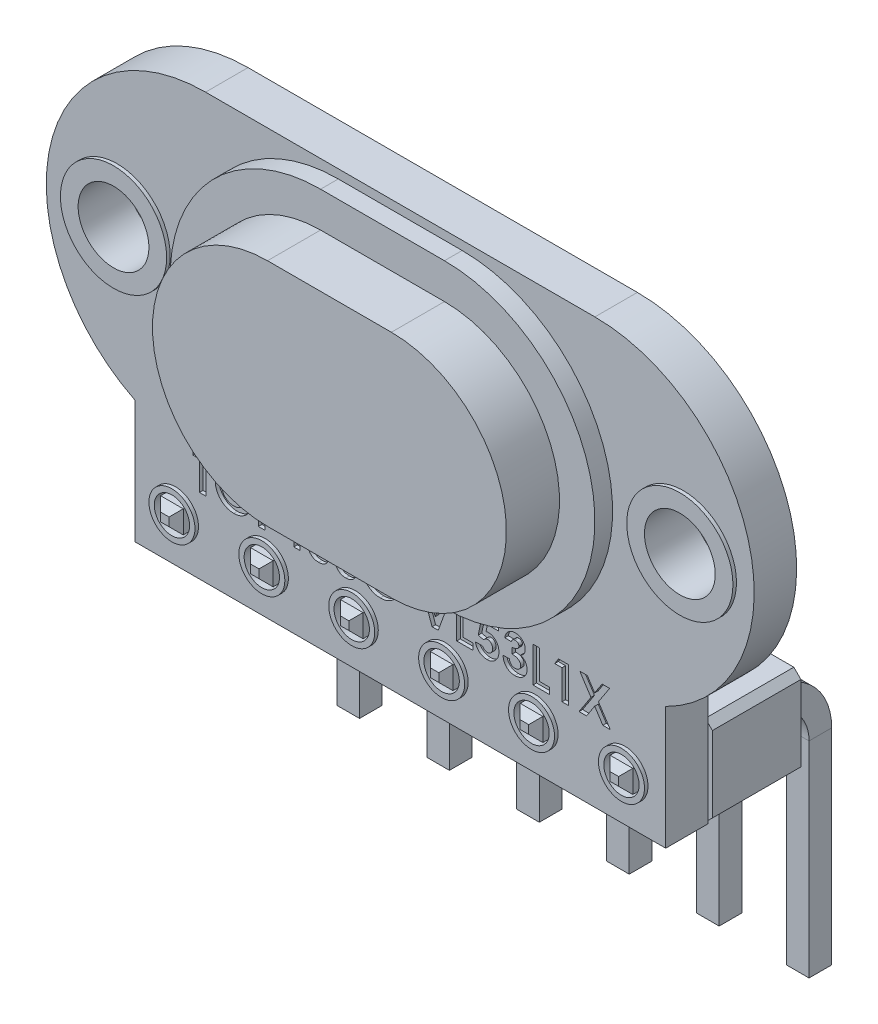
SolidWorks part; units mm, degrees
ref_plane "Plan de face" through (0, 0, 0) normal (0, 0, 1) x (1, 0, 0)
ref_plane "Plan de dessus" through (0, 0, 0) normal (0, 1, 0) x (1, 0, 0)
ref_plane "Plan de droite" through (0, 0, 0) normal (1, 0, 0) x (0, 0, -1)
sketch "Esquisse1" plane through (0, 0, 0) normal (0, 0, 1) x (1, 0, 0)
  line L0 (-7.5, -4.0311) -> (-7.5, -7.5)
  line L1 (0, 19.431) -> (0, -15.0057) construction
  line L2 (-5.5, 0) -> (5.5, 0) construction
  line L5 (-7.5, -7.5) -> (7.5, -7.5)
  line L6 (7.5, -4.0311) -> (7.5, -7.5)
  line L7 (-6.35, -6.23) -> (-3.81, -6.23) construction
  line L8 (-5.5, 4.5) -> (5.5, 4.5)
  circle A2 centre (-8, 0) radius 1
  circle A3 centre (8, 0) radius 1
  circle A4 centre (-6.35, -6.23) radius 0.5
  circle A5 centre (-3.81, -6.23) radius 0.5
  circle A6 centre (-1.27, -6.23) radius 0.5
  circle A7 centre (1.27, -6.23) radius 0.5
  circle A8 centre (3.81, -6.23) radius 0.5
  circle A9 centre (6.35, -6.23) radius 0.5
  arc A10 (-5.5, 4.5) -> (-7.5, -4.0311) centre (-5.5, 0) ccw
  arc A11 (7.5, -4.0311) -> (5.5, 4.5) centre (5.5, 0) ccw
  point P7 (0, 0)
  point P8 (0, 0)
  point P14 (0, 0)
  point P16 (-6.5656, 0)
  point P32 (0, 0)
  point P33 (2.7958, 2.4722)
  point P34 (0, 0)
  point P35 (0, 0)
  point P36 (-7.5, -2.7182)
  point P38 (0, 0)
  dimension "D1" = 20
  dimension "D3" = 2
  dimension "D6" = 1
  dimension "D2" = 16
  dimension "D5" = 4.5
  dimension "D4" = 15
  dimension "D8" = 2.54
  dimension "D9" = 1.27
  dimension "D10" = 12
  dimension "D11" = 8.5311
  dimension "D7" = 6
extrude "Boss.-Extru.1" add sketch "Esquisse1" along normal mid plane 1.2
sketch "Esquisse2" plane through (0, 0, 0.6) normal (0, 0, 1) x (1, 0, 0)
  line L0 (-1.75, 0) -> (1.75, 0) construction
  line L1 (-1.75, 4.25) -> (1.75, 4.25)
  line L2 (-1.75, -4.25) -> (1.75, -4.25)
  arc A0 (-1.75, 4.25) -> (-1.75, -4.25) centre (-1.75, 0) ccw
  arc A1 (1.75, -4.25) -> (1.75, 4.25) centre (1.75, 0) ccw
  point P3 (0, 0)
  point P8 (0, 0)
  dimension "D2" = 12
  dimension "D1" = 8.5
extrude "Boss.-Extru.2" add sketch "Esquisse2" along normal blind 0.5
sketch "Esquisse4" plane through (0, 0, 1.1) normal (0, 0, 1) x (1, 0, 0)
  line L4 (-1.75, -3.25) -> (1.75, -3.25)
  line L5 (1.75, 3.25) -> (-1.75, 3.25)
  line L6 (-1.75, -3.25) -> (1.75, -3.25)
  line L7 (1.75, 3.25) -> (-1.75, 3.25)
  arc A4 (-1.75, 3.25) -> (-1.75, -3.25) centre (-1.75, 0) ccw
  arc A5 (1.75, -3.25) -> (1.75, 3.25) centre (1.75, 0) ccw
  arc A6 (-1.75, 3.25) -> (-1.75, -3.25) centre (-1.75, 0) ccw
  arc A7 (1.75, -3.25) -> (1.75, 3.25) centre (1.75, 0) ccw
  dimension "D1" = 1
extrude "Boss.-Extru.4" add sketch "Esquisse4" along normal blind 1.5
sketch "Esquisse3" plane through (0, 0, 0.6) normal (0, 0, 1) x (1, 0, 0)
  line L0 (-6.35, -6.23) -> (-3.81, -6.23) construction
  circle A0 centre (-8, 0) radius 1.5
  circle A1 centre (8, 0) radius 1.5
  circle A2 centre (8, 0) radius 1 construction
  circle A3 centre (-8, 0) radius 1 construction
  circle A4 centre (8, 0) radius 1
  circle A5 centre (-8, 0) radius 1
  circle A6 centre (-6.35, -6.23) radius 0.65
  circle A7 centre (-6.35, -6.23) radius 0.5 construction
  circle A8 centre (-3.81, -6.23) radius 0.65
  circle A9 centre (-1.27, -6.23) radius 0.65
  circle A10 centre (1.27, -6.23) radius 0.65
  circle A11 centre (3.81, -6.23) radius 0.65
  circle A12 centre (6.35, -6.23) radius 0.65
  circle A13 centre (6.35, -6.23) radius 0.5 construction
  circle A14 centre (3.81, -6.23) radius 0.5 construction
  circle A15 centre (1.27, -6.23) radius 0.5 construction
  circle A16 centre (-1.27, -6.23) radius 0.5 construction
  circle A17 centre (-3.81, -6.23) radius 0.5 construction
  circle A18 centre (6.35, -6.23) radius 0.5
  circle A19 centre (3.81, -6.23) radius 0.5
  circle A20 centre (1.27, -6.23) radius 0.5
  circle A21 centre (-1.27, -6.23) radius 0.5
  circle A22 centre (-3.81, -6.23) radius 0.5
  circle A23 centre (-6.35, -6.23) radius 0.5
  dimension "D1" = 3
  dimension "D2" = 1.3
  dimension "D4" = 2.54
  dimension "D3" = 6
extrude "Boss.-Extru.3" add sketch "Esquisse3" along normal blind 0.1
sketch "Esquisse5" plane through (0, 0, 0.6) normal (0, 0, 1) x (1, 0, 0)
  line L0 (-7.5, -5.3812) -> (7.5, -5.3812) construction
  line L1 (-7.5, -4.0311) -> (-7.5, -7.5) construction
  line L2 (7.5, -7.5) -> (7.5, -4.0311) construction
  text T0 "<b>TOF400C-VL53L1X</b>" font "Century Gothic" height 1
  point P7 (7.5, -5.2129)
  point P8 (7.5, -5.3812)
extrude "Enlèv. mat.-Extru.1" cut sketch "Esquisse5" against normal blind 0.1
mirror "Symétrie1" about plane through (0, 0, 0) normal (0, 0, 1) of "Boss.-Extru.3"
sketch "Esquisse6" plane through (0, 0, -0.6) normal (0, 0, -1) x (-1, 0, 0)
  line L0 (-5.5521, -5.2944) -> (-5.5521, 1.9609) construction
  text T0 "<b>VIN</b>\r\n<b>GND</b>\r\n<b>SDA</b>\r\n<b>SCL</b>\r\n<b>INT</b>\r\n<b>SHUT</b>" font "Century Gothic" height 1.46
  point P3 (-5.2543, 8.2569)
  point P4 (-5.5521, 1.9609)
  point P5 (-6.1801, 8.4762)
extrude "Enlèv. mat.-Extru.2" cut sketch "Esquisse6" against normal blind 0.1
sketch "Esquisse7" plane through (0, 0, -0.6) normal (0, 0, -1) x (-1, 0, 0)
  line L0 (-7.62, -5.16) -> (-7.42, -4.96)
  line L1 (-7.42, -7.5) -> (-5.28, -7.5)
  line L2 (-7.62, -7.3) -> (-7.62, -5.16)
  line L3 (-7.42, -4.96) -> (-5.28, -4.96)
  line L4 (-5.08, -7.3) -> (-5.08, -5.16)
  line L5 (-7.62, -7.5) -> (-5.08, -4.96) construction
  line L6 (-7.62, -4.96) -> (-5.08, -7.5) construction
  line L7 (-5.28, -4.96) -> (-5.08, -5.16)
  line L8 (-5.28, -7.5) -> (-5.08, -7.3)
  line L9 (-7.62, -7.3) -> (-7.42, -7.5)
  point P0 (-6.35, -6.23)
  dimension "D1" = 2.54
extrude "Boss.-Extru.5" add sketch "Esquisse7" along normal blind 2.5
ref_plane "Plan1" through (6.35, 0, 0) normal (1, 0, 0) x (0, 0, -1)
sketch "Esquisse8" plane through (6.35, 0, 0) normal (1, 0, 0) x (0, 0, -1)
  line L0 (-0.9, -6.23) -> (3.1, -6.23)
  line L1 (4.6, -7.73) -> (4.6, -13.73)
  line L2 (3.1, -4.96) -> (0.6, -4.96) construction
  line L3 (3.1, -7.5) -> (0.6, -7.5) construction
  line L4 (3.1, -5.16) -> (3.1, -7.3) construction
  arc A0 (3.1, -6.23) -> (4.6, -7.73) centre (3.1, -7.73) cw
  point P9 (-1.0598, -6.23)
  point P10 (3.1, -6.23)
  dimension "D3" = 4
  dimension "D1" = 7.5
  dimension "D2" = 6
ref_plane "Plan2" through (6.35, -13.73, -4.6) normal (0, -1, 0) x (-1, 0, 0)
sketch "Esquisse9" plane through (6.35, -13.73, -4.6) normal (0, -1, 0) x (-1, 0, 0)
  line L1 (0.32, -0.32) -> (-0.32, -0.32)
  line L2 (0.32, -0.32) -> (0.32, 0.32)
  line L3 (0.32, 0.32) -> (-0.32, 0.32)
  line L4 (-0.32, -0.32) -> (-0.32, 0.32)
  line L5 (0.32, -0.32) -> (-0.32, 0.32) construction
  line L6 (0.32, 0.32) -> (-0.32, -0.32) construction
  point P0 (0, 0)
  dimension "D1" = 0.64
sweep "Balayage1" add profiles "Esquisse9" path "Esquisse8"
chamfer "Chanfrein1" distance 0.2 angle 45 8 edges at (6.35, -6.55, 0.9) (6.03, -6.23, 0.9) (6.35, -5.91, 0.9) (6.67, -6.23, 0.9) (6.35, -13.73, -4.92) (6.03, -13.73, -4.6) (6.35, -13.73, -4.28) (6.67, -13.73, -4.6)
pattern_linear "Répétition linéaire2" count 6 spacing 2.54 along (-1, 0, 0) of "Boss.-Extru.5", "Balayage1", "Chanfrein1"
